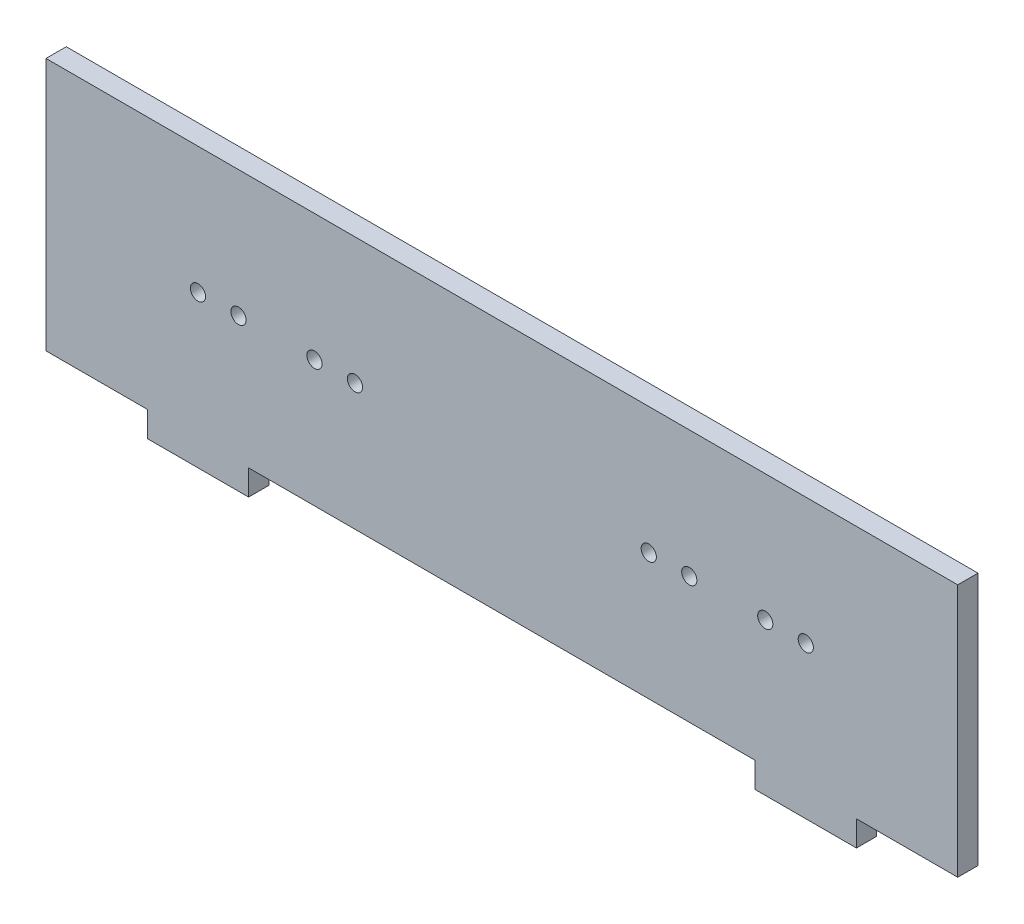
SolidWorks part; units mm, degrees
material "Acrylic (Medium-high impact)"
ref_plane "Front Plane" through (0, 0, 0) normal (0, 0, 1) x (1, 0, 0)
ref_plane "Top Plane" through (0, 0, 0) normal (0, 1, 0) x (1, 0, 0)
ref_plane "Right Plane" through (0, 0, 0) normal (1, 0, 0) x (0, 0, -1)
sketch "Sketch1" plane through (0, 0, 0) normal (0, 0, 1) x (1, 0, 0)
  line L0 (-47.2994, -31.1171) -> (52.7006, -31.1171)
  line L1 (72.7006, -31.1171) -> (92.7006, -31.1171)
  line L2 (-87.2994, 18.8829) -> (92.7006, 18.8829)
  line L3 (-87.2994, 18.8829) -> (-87.2994, -31.1171)
  line L4 (-87.2994, -31.1171) -> (-67.2994, -31.1171)
  line L5 (92.7006, 18.8829) -> (92.7006, -31.1171)
  line L6 (-67.2994, -31.1171) -> (-67.2994, -36.1171)
  line L7 (-67.2994, -36.1171) -> (-47.2994, -36.1171)
  line L8 (-47.2994, -31.1171) -> (-47.2994, -36.1171)
  line L10 (52.7006, -31.1171) -> (52.7006, -36.1171)
  line L11 (52.7006, -36.1171) -> (72.7006, -36.1171)
  line L12 (72.7006, -31.1171) -> (72.7006, -36.1171)
  circle A0 centre (-57.2994, -6.1171) radius 1.5
  circle A1 centre (62.7006, -6.1171) radius 1.5
  circle A4 centre (-49.2994, -6.1171) radius 1.5
  circle A5 centre (54.7006, -6.1171) radius 1.5
  circle A6 centre (-34.2994, -6.1171) radius 1.5
  circle A7 centre (-26.2994, -6.1171) radius 1.5
  circle A8 centre (39.7006, -6.1171) radius 1.5
  circle A9 centre (31.7006, -6.1171) radius 1.5
  dimension "D1" = 30
  dimension "D10" = 180
  dimension "D11" = 8
  dimension "D12" = 8
  dimension "D13" = 8
  dimension "D15" = 8
  dimension "D17" = 15
  dimension "D3" = 15
  dimension "D2" = 20
  dimension "D4" = 30
  dimension "D5" = 25
  dimension "D6" = 25
  dimension "D7" = 50
  dimension "D8" = 100
extrude "Boss-Extrude1" add sketch "Sketch1" along normal blind 4
